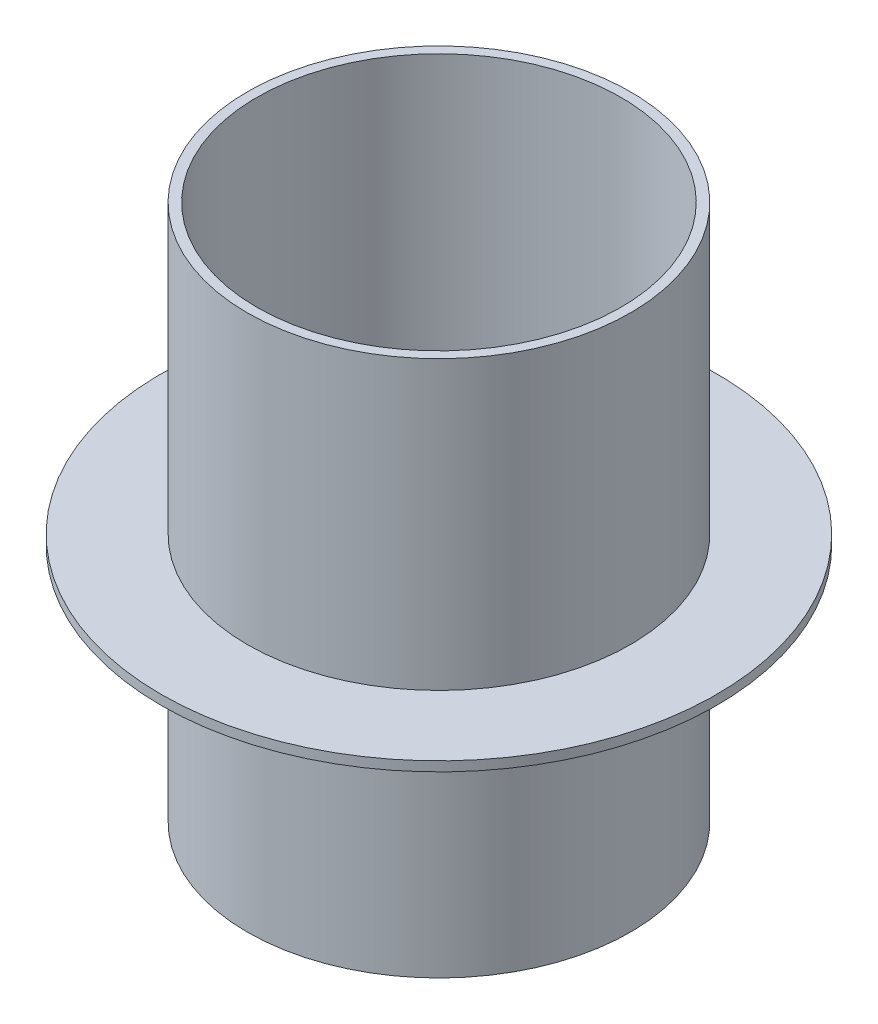
SolidWorks part; units mm, degrees
ref_plane "前视基准面" through (0, 0, 0) normal (0, 0, 1) x (1, 0, 0)
ref_plane "上视基准面" through (0, 0, 0) normal (0, 1, 0) x (1, 0, 0)
ref_plane "右视基准面" through (0, 0, 0) normal (1, 0, 0) x (0, 0, -1)
sketch "草图1" plane through (0, 0, 0) normal (0, 0, 1) x (1, 0, 0)
  line L0 (40, 112) -> (40, 52)
  line L1 (40, 52) -> (58, 52)
  line L2 (58, 52) -> (58, 50)
  line L3 (58, 50) -> (40, 50)
  line L4 (40, 50) -> (40, 0)
  line L5 (40, 0) -> (38, 0)
  line L6 (38, 50) -> (38, 112)
  line L7 (38, 112) -> (40, 112)
  line L8 (0, 71.2248) -> (0, -38.6058) construction
  line L10 (38, 50) -> (38, 0)
  dimension "D1" = 40
  dimension "D2" = 2
  dimension "D3" = 2
  dimension "D4" = 2
  dimension "D5" = 60
  dimension "D6" = 50
  dimension "D8" = 50
revolve "旋转1" add sketch "草图1" angle 360 about L8
